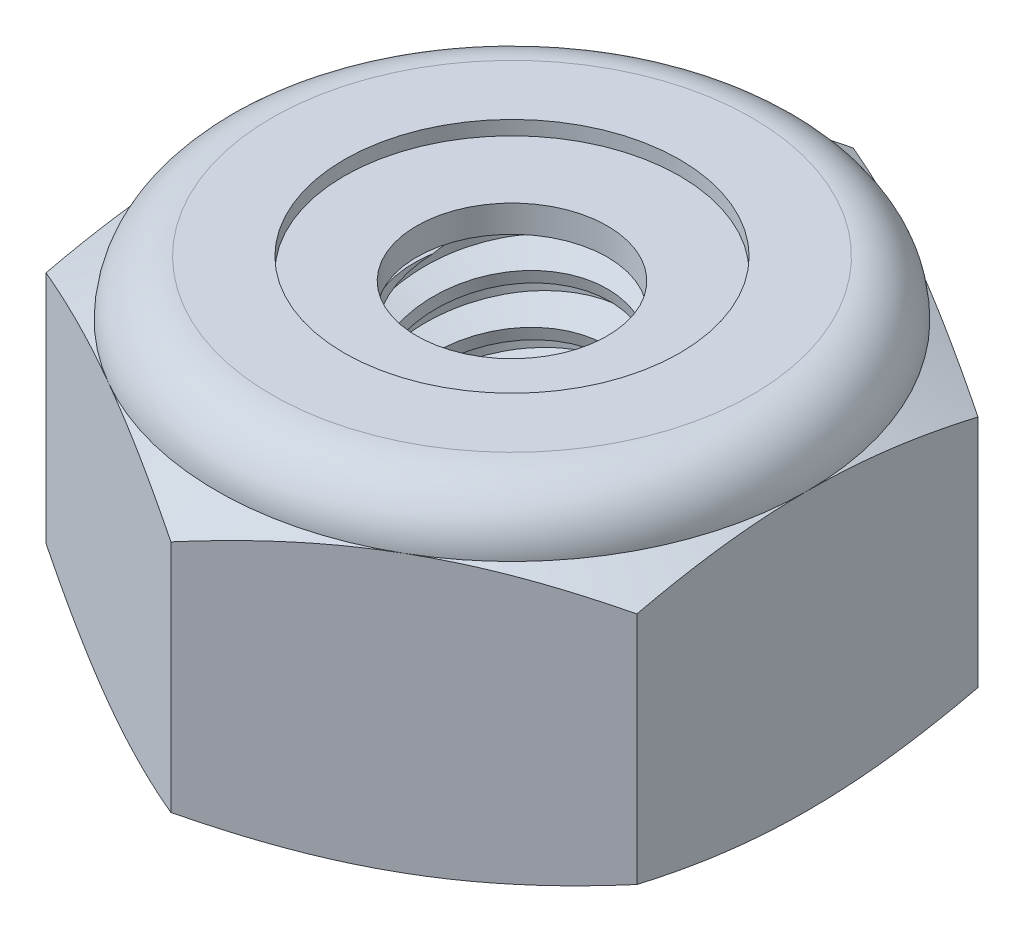
SolidWorks part; units mm, degrees
ref_plane "Front" through (0, 0, 0) normal (0, 0, 1) x (1, 0, 0)
ref_plane "Top" through (0, 0, 0) normal (0, 1, 0) x (1, 0, 0)
ref_plane "Right" through (0, 0, 0) normal (1, 0, 0) x (0, 0, -1)
sketch "Sketch1" plane through (0, 0, 0) normal (0, 1, 0) x (1, 0, 0)
  line L1 (0, 3.6662) -> (-3.175, 1.8331)
  line L2 (-3.175, 1.8331) -> (-3.175, -1.8331)
  line L3 (-3.175, -1.8331) -> (0, -3.6662)
  line L4 (0, -3.6662) -> (3.175, -1.8331)
  line L5 (3.175, -1.8331) -> (3.175, 1.8331)
  line L6 (3.175, 1.8331) -> (0, 3.6662)
  circle A0 centre (0, 0) radius 3.175 construction
  dimension "Hex Flats" = 6.35
extrude "Extrude1" add sketch "Sketch1" along normal blind 3.5719
sketch "Sketch2" plane through (0, 0, 0) normal (1, 0, 0) x (0, 0, -1)
  line L0 (-1.2573, 0) -> (-1.2573, 3.5719) construction
  line L1 (0, 0) -> (1.2573, 0)
  line L2 (0, 0) -> (0, 3.5719)
  line L3 (0, 3.5719) -> (1.2573, 3.5719)
  line L4 (1.2573, 0) -> (1.2573, 3.5719)
  line L5 (-1.8331, 3.5719) -> (1.8331, 3.5719) construction
  line L7 (0, -1.2573) -> (0, 0) construction
  dimension "Thread Dia" = 2.5146
revolve "Revolve1" add sketch "Sketch2" angle 360 about L7
sketch "Sketch3" plane through (0, 0, 0) normal (1, 0, 0) x (0, 0, -1)
  line L0 (1.2573, 3.5719) -> (-1.2573, 3.5719) construction
  line L1 (-1.2573, 3.5719) -> (-1.2573, 3.0427) construction
  line L2 (-1.2573, 3.0427) -> (1.2573, 3.5719) construction
  line L3 (1.2573, 3.5719) -> (1.2709, 3.5071) construction
  line L4 (1.2709, 3.5071) -> (1.3663, 3.054)
  line L5 (1.3663, 3.054) -> (1.0519, 3.1569)
  line L6 (1.0519, 3.1569) -> (1.0247, 3.2863)
  line L7 (1.0247, 3.2863) -> (1.2709, 3.5071)
  line L8 (1.0383, 3.2216) -> (1.3186, 3.2806) construction
  line L9 (1.2573, 3.5719) -> (1.2573, 3.2677) construction
  line L10 (1.2573, 3.2677) -> (-1.2573, 2.7385) construction
  line L11 (-1.2573, 2.7385) -> (-1.2573, 3.0427) construction
  line L12 (-0.1197, 3.5719) -> (0.1197, 2.4344) construction
  line L13 (-1.2573, 0) -> (-1.2573, 3.5719) construction
  line L14 (0, 3.5719) -> (1.2573, 3.5719) construction
  line L15 (1.2573, 0) -> (1.2573, 3.5719) construction
  point P13 (0, 3.0031)
  dimension "D1" = 0.0661
  dimension "D2" = 0.1323
  dimension "Thread Pitch" = 0.5292
  dimension "D4" = 60
  dimension "D5" = 0.5292
revolve "Cut-Revolve1" cut sketch "Sketch3" angle 360 about L12
pattern_linear "LPattern1" count 7 spacing 0.5292 along (0, -1, 0) count 2 spacing 0.5292 along (0, 1, 0) of "Cut-Revolve1"
sketch "Sketch4" plane through (0, 0, 0) normal (1, 0, 0) x (0, 0, -1)
  line L0 (0, 3.5719) -> (1.2573, 3.5719)
  line L1 (1.2573, 3.5719) -> (1.0247, 3.4634)
  line L2 (1.0247, 3.4634) -> (1.0247, 0.1085)
  line L3 (1.0247, 0.1085) -> (1.2573, 0)
  line L4 (1.2573, 0) -> (0, 0)
  line L5 (0, 0) -> (0, 3.5719)
  line L6 (1.2573, 0) -> (1.2573, 3.5719) construction
  line L7 (0, 3.5719) -> (1.2573, 3.5719) construction
  line L8 (0, 0) -> (1.2573, 0) construction
  line L9 (0, 0) -> (0, 3.5719) construction
  line L10 (0, 3.5719) -> (0, 3.8285) construction
  dimension "D1" = 25
revolve "Cut-Revolve2" cut sketch "Sketch4" angle 360 about L10
combine bodies "Combine1" operation type subtract main body 112 bodies to subtract 111
sketch "Sketch5" plane through (0, 0, 0) normal (1, 0, 0) x (0, 0, -1)
  line L0 (0, 0) -> (3.175, 0)
  line L1 (3.175, 0) -> (3.6662, 0.229)
  line L2 (3.6662, 0.229) -> (3.6662, 2.7475)
  line L3 (3.6662, 2.7475) -> (3.175, 2.9766)
  line L4 (2.5797, 3.5719) -> (2.5797, 4.8419)
  line L5 (2.5797, 4.8419) -> (4.9362, 4.8419)
  line L6 (4.9362, 4.8419) -> (4.9362, -1.27)
  line L7 (4.9362, -1.27) -> (0, -1.27)
  line L8 (0, -1.27) -> (0, 0)
  line L9 (3.175, 2.9766) -> (3.175, 0) construction
  line L10 (0, 0) -> (1.2573, 0) construction
  line L13 (3.6662, 1.4883) -> (4.9362, 1.4883) construction
  line L14 (3.6662, 3.5719) -> (3.6662, 0) construction
  line L15 (0, 0) -> (0, 4.8419) construction
  line L20 (0, 4.8419) -> (2.5797, 4.8419) construction
  line L22 (0, 3.5719) -> (1.2573, 3.5719) construction
  arc A0 (3.175, 2.9766) -> (2.5797, 3.5719) centre (2.5797, 2.9766) ccw
  dimension "D1" = 25
  dimension "D2" = 1.27
  dimension "D3" = 3.5719
  dimension "D4" = 0.5953
revolve "Cut-Revolve3" cut sketch "Sketch5" angle 360 about L15
sketch "Sketch6" plane through (0, 0, 0) normal (1, 0, 0) x (0, 0, -1)
  line L0 (0, 2.9766) -> (3.0226, 2.9766)
  line L1 (2.5797, 3.4195) -> (1.8022, 3.4195)
  line L2 (0, 4.8419) -> (0, 2.9766)
  line L3 (1.8022, 4.8419) -> (0, 4.8419)
  line L4 (0, 4.8419) -> (2.5797, 4.8419) construction
  line L5 (0, 0) -> (0, 4.8419) construction
  line L6 (0, 4.8419) -> (0, 44.323) construction
  line L7 (1.8022, 3.4195) -> (1.8022, 4.8419)
  line L8 (2.5797, 3.5719) -> (2.5797, 3.4195) construction
  line L9 (1.8022, 3.4195) -> (1.0247, 3.4195) construction
  line L10 (1.0247, 3.4195) -> (1.0247, 3.4634) construction
  arc A0 (3.0226, 2.9766) -> (2.5797, 3.4195) centre (2.5797, 2.9766) ccw
  arc A1 (3.175, 2.9766) -> (2.5797, 3.5719) centre (2.5797, 2.9766) ccw construction
  dimension "D1" = 0.1524
revolve "Cut-Revolve4" cut sketch "Sketch6" angle 360 about L6
sketch "Sketch7" plane through (0, 0, 0) normal (1, 0, 0) x (0, 0, -1)
  line L0 (1.0247, 3.0528) -> (2.9384, 3.0528)
  line L1 (2.5797, 3.3433) -> (1.0247, 3.3433)
  line L2 (1.0247, 3.3433) -> (1.0247, 3.0528)
  line L3 (1.0247, 3.0528) -> (0, 3.0528) construction
  line L4 (0, 3.0528) -> (0, 3.3433) construction
  line L5 (0, 3.3433) -> (1.0247, 3.3433) construction
  line L6 (1.0247, 3.0528) -> (1.0247, 2.9766) construction
  line L7 (0, 2.9766) -> (3.0226, 2.9766) construction
  line L8 (2.5797, 3.3433) -> (2.5797, 3.4195) construction
  arc A0 (2.9384, 3.0528) -> (2.5797, 3.3433) centre (2.5797, 2.9766) ccw
  arc A2 (3.0226, 2.9766) -> (2.5797, 3.4195) centre (2.5797, 2.9766) ccw construction
  dimension "D1" = 0.0762
revolve "Revolve2" add sketch "Sketch7" angle 360 about L4
equation "\"D1@Sketch3\"=\"Thread Pitch@Sketch3\"/8"
equation "\"D2@Sketch3\"=\"Thread Pitch@Sketch3\"/4"
equation "\"D5@Sketch3\"=\"Thread Pitch@Sketch3\""
equation "\"D4@LPattern1\"=\"Thread Pitch@Sketch3\""
equation "\"D3@LPattern1\"=\"Thread Pitch@Sketch3\""
equation "\"D1@LPattern1\"=\"Height@Extrude1\"/\"Thread Pitch@Sketch3\""
equation "\"D4@Sketch5\"=\"Height@Extrude1\"/6"
